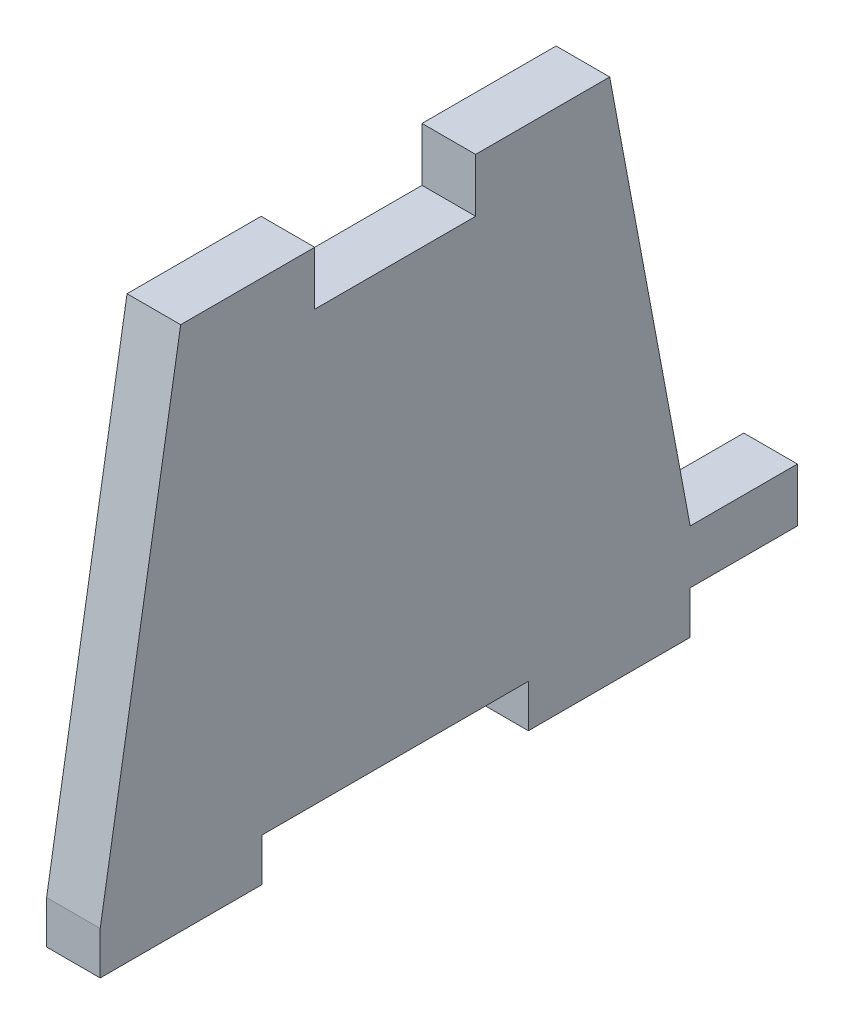
SolidWorks part; units mm, degrees
ref_plane "Front Plane" through (0, 0, 0) normal (0, 0, 1) x (1, 0, 0)
ref_plane "Top Plane" through (0, 0, 0) normal (0, 1, 0) x (1, 0, 0)
ref_plane "Right Plane" through (0, 0, 0) normal (1, 0, 0) x (0, 0, -1)
sketch "Sketch1" plane through (0, 0, 0) normal (1, 0, 0) x (0, 0, -1)
  line L1 (23.8125, 0) -> (23.8125, 3.175)
  line L2 (23.8125, 3.175) -> (17.4625, 3.175)
  line L3 (17.4625, 3.175) -> (12.7, 28.575)
  line L6 (12.7, 28.575) -> (4.7625, 28.575)
  line L7 (-12.7, 28.575) -> (-17.4625, 0)
  line L10 (-4.7625, 28.575) -> (-12.7, 28.575)
  line L11 (-4.7625, 25.4) -> (4.7625, 25.4)
  line L12 (-4.7625, 25.4) -> (-4.7625, 28.575)
  line L14 (4.7625, 25.4) -> (4.7625, 28.575)
  line L15 (-17.4625, 0) -> (-17.4625, -2.54)
  line L16 (-17.4625, -2.54) -> (-7.8867, -2.54)
  line L17 (-7.8867, -2.54) -> (-7.8867, 0)
  line L18 (7.8867, 0) -> (7.8867, -2.54)
  line L19 (7.8867, -2.54) -> (17.4625, -2.54)
  line L20 (17.4625, -2.54) -> (17.4625, 0)
  line L21 (-7.8867, 0) -> (7.8867, 0)
  line L22 (17.4625, 0) -> (23.8125, 0)
  point P0 (0, 25.4)
  point P2 (0, 0)
  point P3 (0, 0)
  point P4 (0, 0)
  dimension "D4" = 25.4
  dimension "D5" = 6.35
  dimension "D6" = 9.525
  dimension "D7" = 3.175
  dimension "D8" = 9.5758
  dimension "D10" = 9.5758
  dimension "D9" = 3.175
  dimension "D11" = 2.54
  dimension "D12" = 25.4
  dimension "D2" = 34.925
extrude "Boss-Extrude1" add sketch "Sketch1" along normal mid plane 3.175 contours L7 L15 L16 L17 L21 L18 L19 L20 L22 L1 L2 L3 L6 L14 L11 L12 L10
equation "\"D8@Sketch1\"=0.375+0.002"
